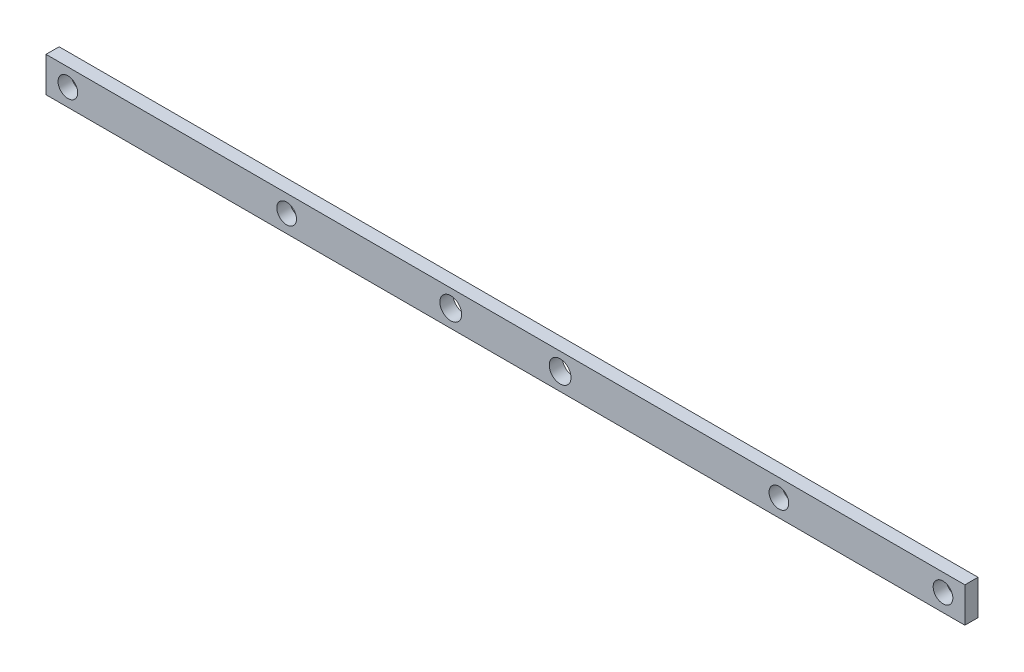
SolidWorks part; units mm, degrees
ref_plane "Front Plane" through (0, 0, 0) normal (0, 0, 1) x (1, 0, 0)
ref_plane "Top Plane" through (0, 0, 0) normal (0, 1, 0) x (1, 0, 0)
ref_plane "Right Plane" through (0, 0, 0) normal (1, 0, 0) x (0, 0, -1)
sketch "Sketch1" plane through (0, 0, 0) normal (0, 0, 1) x (1, 0, 0)
  line L0 (-126.0191, 0) -> (128.8932, 0) construction
  line L5 (-105, -4) -> (105, -4)
  line L6 (-105, -4) -> (-105, 4)
  line L7 (-105, 4) -> (105, 4)
  line L8 (105, -4) -> (105, 4)
  circle A0 centre (-12.5, 0) radius 2.49
  circle A1 centre (12.5, 0) radius 2.49
  circle A2 centre (-100, 0) radius 2.25
  circle A3 centre (100, 0) radius 2.25
  circle A4 centre (-50, 0) radius 2.25
  circle A5 centre (62.5, 0) radius 2.25
  point P0 (0, 0)
  dimension "D3" = 4.98
  dimension "D10" = 4.98
  dimension "D12" = 4.5
  dimension "D13" = 4
  dimension "D16" = 4.5
  dimension "D17" = 50
  dimension "D18" = 4.5
  dimension "D19" = 50
  dimension "D20" = 4.5
  dimension "D1" = 8
  dimension "D2" = 210
  dimension "D4" = 12.5
  dimension "D5" = 105
  dimension "D6" = 4
  dimension "D7" = 4
  dimension "D8" = 12.5
  dimension "D9" = 4
  dimension "D11" = 100
  dimension "D14" = 100
  dimension "D15" = 4
  dimension "D21" = 4
extrude "Boss-Extrude1" add sketch "Sketch1" along normal blind 3
